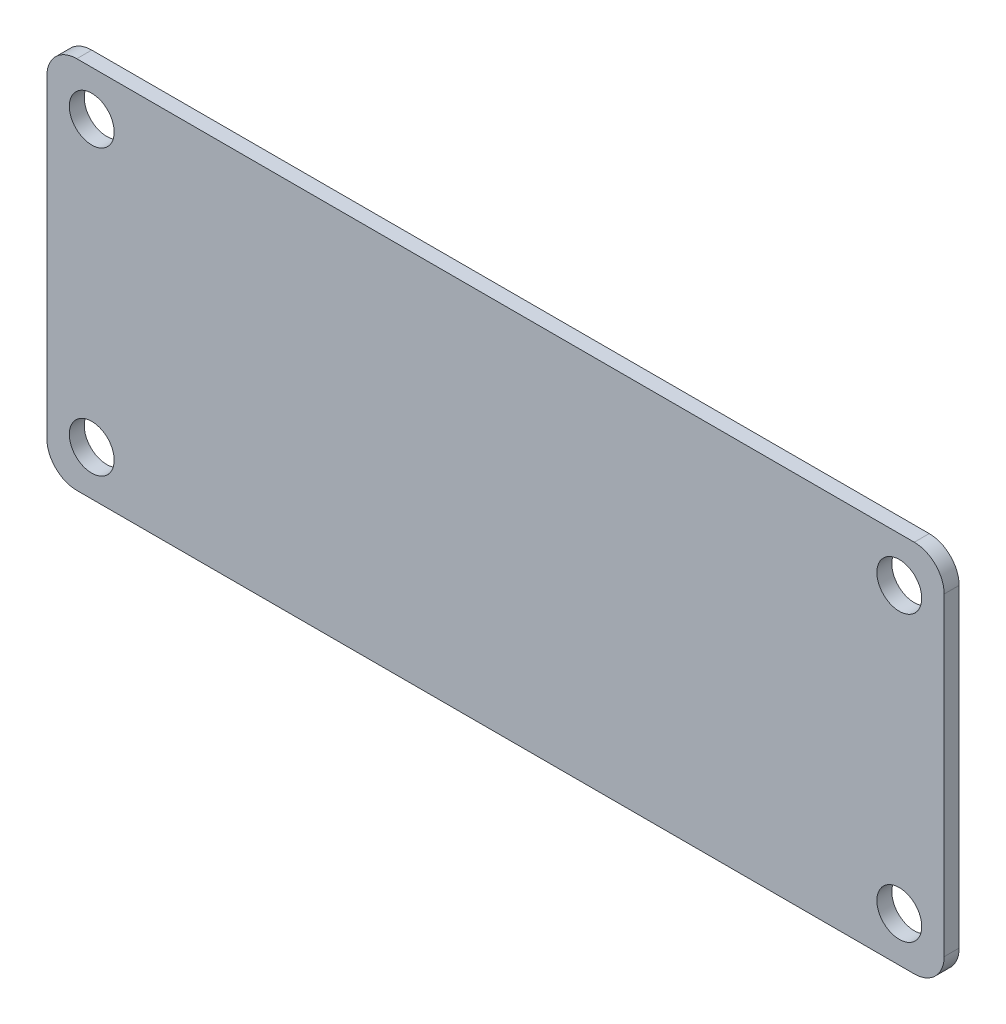
SolidWorks part; units mm, degrees
ref_plane "正面" through (0, 0, 0) normal (0, 0, 1) x (1, 0, 0)
ref_plane "平面" through (0, 0, 0) normal (0, 1, 0) x (1, 0, 0)
ref_plane "右側面" through (0, 0, 0) normal (1, 0, 0) x (0, 0, -1)
sketch "ｽｹｯﾁ1" plane through (0, 0, 0) normal (0, 0, 1) x (1, 0, 0)
  line L1 (-30, 12.5) -> (30, 12.5)
  line L2 (-30, 12.5) -> (-30, -12.5)
  line L3 (-30, -12.5) -> (30, -12.5)
  line L4 (30, 12.5) -> (30, -12.5)
  dimension "D1" = 60
  dimension "D2" = 30
  dimension "D3" = 25
  dimension "D4" = 12.5
extrude "ﾎﾞｽ - 押し出し1" add sketch "ｽｹｯﾁ1" along normal blind 1
sketch "ｽｹｯﾁ2" plane through (0, 0, 1) normal (0, 0, 1) x (1, 0, 0)
  line L0 (30, 12.5) -> (-30, 12.5) construction
  line L1 (-30, 12.5) -> (-30, -12.5) construction
  line L2 (30, -12.5) -> (30, 12.5) construction
  line L3 (-30, -12.5) -> (30, -12.5) construction
  circle A0 centre (-27, 9.5) radius 1.5
  circle A1 centre (27, 9.5) radius 1.5
  circle A2 centre (-27, -9.5) radius 1.5
  circle A3 centre (27, -9.5) radius 1.5
  dimension "D1" = 3
  dimension "D2" = 3
  dimension "D7" = 3
  dimension "D8" = 3
  dimension "D3" = 3
  dimension "D4" = 3
  dimension "D5" = 3
  dimension "D6" = 3
  dimension "D9" = 3
  dimension "D10" = 3
  dimension "D11" = 3
  dimension "D12" = 3
extrude "ｶｯﾄ - 押し出し1" cut sketch "ｽｹｯﾁ2" against normal through all
fillet "ﾌｨﾚｯﾄ1" radius 2 4 edges at (30, -12.5, 0.5) (30, 12.5, 0.5) (-30, -12.5, 0.5) (-30, 12.5, 0.5)
